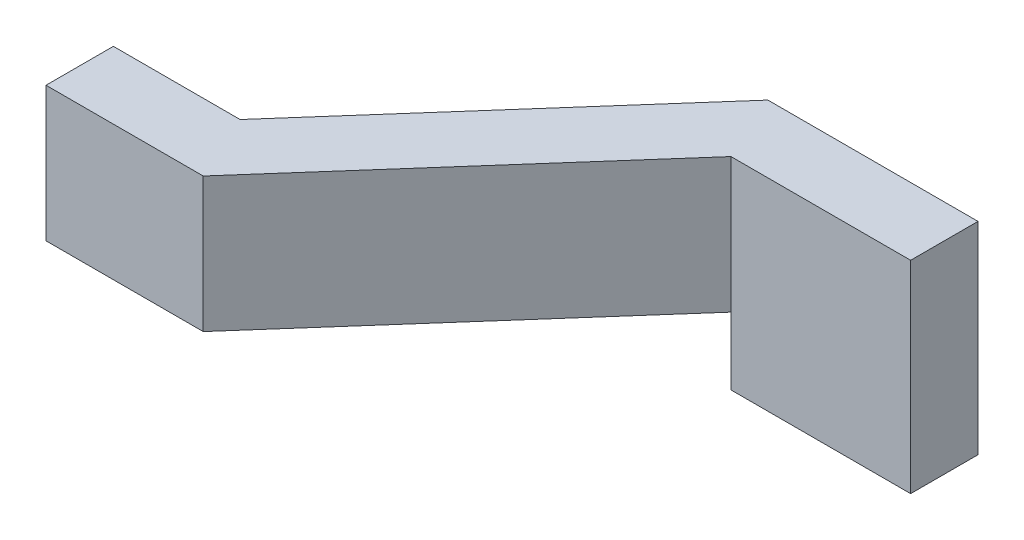
SolidWorks part; units mm, degrees
ref_plane "Front Plane" through (0, 0, 0) normal (0, 0, 1) x (1, 0, 0)
ref_plane "Top Plane" through (0, 0, 0) normal (0, 1, 0) x (1, 0, 0)
ref_plane "Right Plane" through (0, 0, 0) normal (1, 0, 0) x (0, 0, -1)
sketch "Sketch1" plane through (0, 0, 0) normal (0, 1, 0) x (1, 0, 0)
  line L0 (0, 0) -> (0.889, 0)
  line L1 (0.889, 0) -> (2.286, 1.5875)
  line L2 (2.286, 1.5875) -> (3.302, 1.5875)
  line L3 (3.302, 1.5875) -> (3.302, 1.9685)
  line L4 (0, 0) -> (0, 0.381)
  line L5 (0.7168, 0.381) -> (2.1138, 1.9685)
  line L6 (1.6109, 0.8204) -> (1.3249, 1.0721) construction
  line L7 (0, 0.381) -> (0.7168, 0.381)
  line L8 (3.302, 1.9685) -> (2.1138, 1.9685)
  dimension "D1" = 3.302
  dimension "D2" = 0.381
  dimension "D3" = 0.889
  dimension "D4" = 1.016
  dimension "D5" = 1.9685
extrude "Boss-Extrude1" add sketch "Sketch1" along normal mid plane 1.524
sketch "Sketch2" plane through (0, 0, -1.9685) normal (0, 0, -1) x (-1, 0, 0)
  line L0 (-2.286, 0.762) -> (-2.286, -0.762) construction
  line L1 (0, 0.762) -> (-2.286, 0.762)
  line L2 (0, 0.762) -> (0, 0.381)
  line L3 (0, 0.381) -> (-2.286, 0.381)
  line L4 (-2.286, 0.762) -> (-2.286, 0.381)
  line L6 (0.8071, 0) -> (-0.8071, 0) construction
  dimension "D1" = 0.381
extrude "Cut-Extrude1" cut sketch "Sketch2" against normal through all
mirror "Mirror1" about plane through (0, 0, 0) normal (0, 1, 0) of "Cut-Extrude1"
ref_plane "Plane1" through (0, 0, -1.778) normal (0, 0, -1) x (-1, 0, 0)
sketch "Sketch4" plane through (0, 0, -1.9685) normal (0, 0, -1) x (-1, 0, 0)
  line L1 (-3.302, 0.762) -> (-2.286, 0.762)
  line L2 (-3.302, 0.762) -> (-3.302, 0.381)
  line L3 (-3.302, 0.381) -> (-2.286, 0.381)
  line L4 (-2.286, 0.762) -> (-2.286, 0.381)
extrude "Cut-Extrude3" cut sketch "Sketch4" against normal through all
